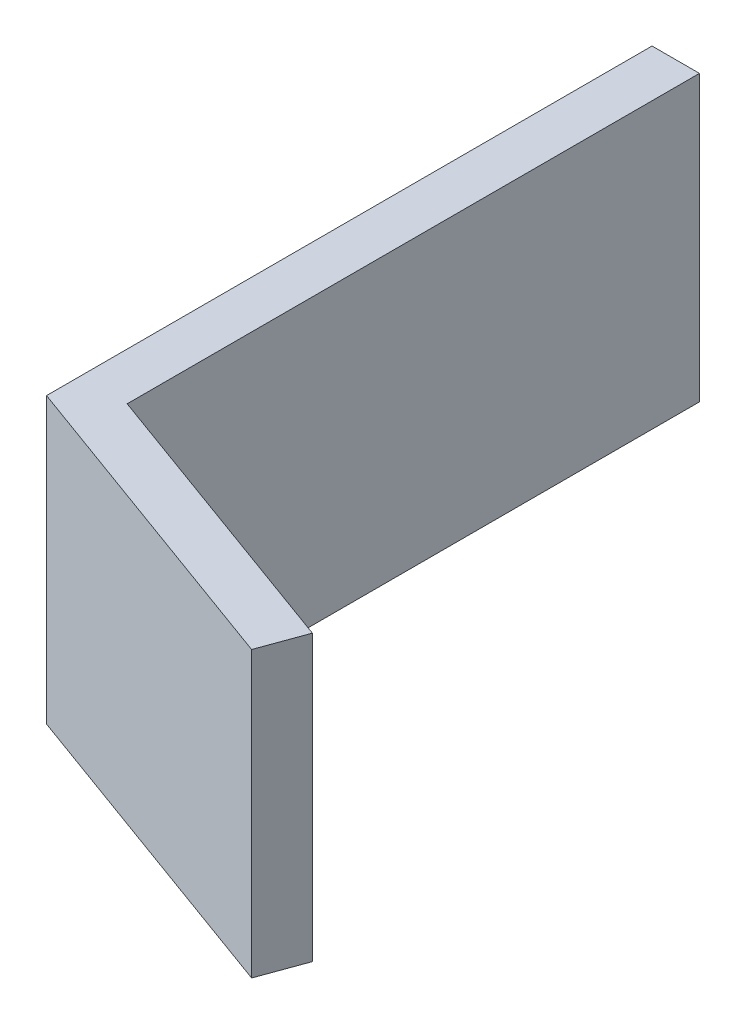
SolidWorks part; units mm, degrees
ref_plane "Front Plane" through (0, 0, 0) normal (0, 0, 1) x (1, 0, 0)
ref_plane "Top Plane" through (0, 0, 0) normal (0, 1, 0) x (1, 0, 0)
ref_plane "Right Plane" through (0, 0, 0) normal (1, 0, 0) x (0, 0, -1)
sketch "Sketch1" plane through (0, 0, 0) normal (0, 1, 0) x (1, 0, 0)
  line L0 (-47.9713, -10.7359) -> (-47.9713, -51.2811)
  line L1 (-47.9713, -51.2811) -> (-26.3813, -59.1392)
  line L2 (-26.3813, -59.1392) -> (-25.2954, -56.1556)
  line L3 (-25.2954, -56.1556) -> (-44.7963, -49.0579)
  line L4 (-44.7963, -49.0579) -> (-44.7963, -10.7359)
  line L5 (-44.7963, -10.7359) -> (-47.9713, -10.7359)
  dimension "D1" = 3.175
  dimension "D2" = 3.175
  dimension "D3" = 21.59
  dimension "D4" = 38.1
  dimension "D5" = 110
extrude "Boss-Extrude1" add sketch "Sketch1" along normal blind 19.05
